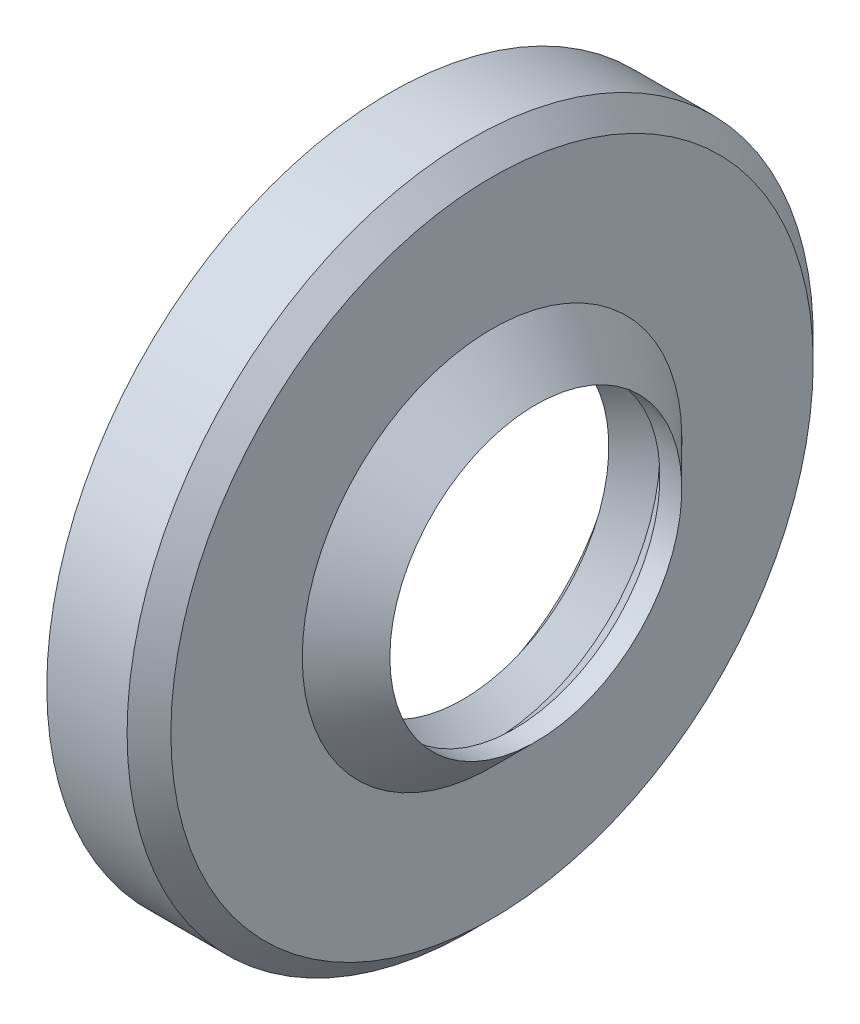
SolidWorks part; units mm, degrees
material "AISI 1020"
ref_plane "Спереди" through (0, 0, 0) normal (0, 0, 1) x (1, 0, 0)
ref_plane "Сверху" through (0, 0, 0) normal (0, 1, 0) x (1, 0, 0)
ref_plane "Справа" through (0, 0, 0) normal (1, 0, 0) x (0, 0, -1)
sketch "Эскиз1" plane through (0, 0, 0) normal (0, 0, 1) x (1, 0, 0)
  line L0 (-1000, 0) -> (49000, 0) construction
  line L1 (0, 22) -> (0, 23.5)
  line L2 (0, 23.5) -> (5.5, 23.5)
  line L3 (5.5, 23.5) -> (7, 22)
  line L4 (7, 22) -> (7, 13)
  line L5 (7, 13) -> (10, 10)
  line L6 (10, 10) -> (8.5, 10)
  line L7 (8.5, 10) -> (7, 11.5)
  line L8 (7, 11.5) -> (5, 10)
  line L9 (5, 10) -> (2.75, 13)
  line L10 (2.75, 13) -> (2.75, 14.5)
  line L11 (2.75, 14.5) -> (5.5, 14.5)
  line L12 (5.5, 14.5) -> (5.5, 22)
  line L14 (5.5, 22) -> (0, 22)
  line L15 (5.5, 22) -> (7, 22) construction
  point P31 (2.75, 22)
  dimension "D1" = 45
  dimension "D2" = 20
  dimension "D3" = 47
  dimension "D4" = 1.5
  dimension "D5" = 10
  dimension "D6" = 7
revolve "Повернуть1" add sketch "Эскиз1" angle 360 about L0
